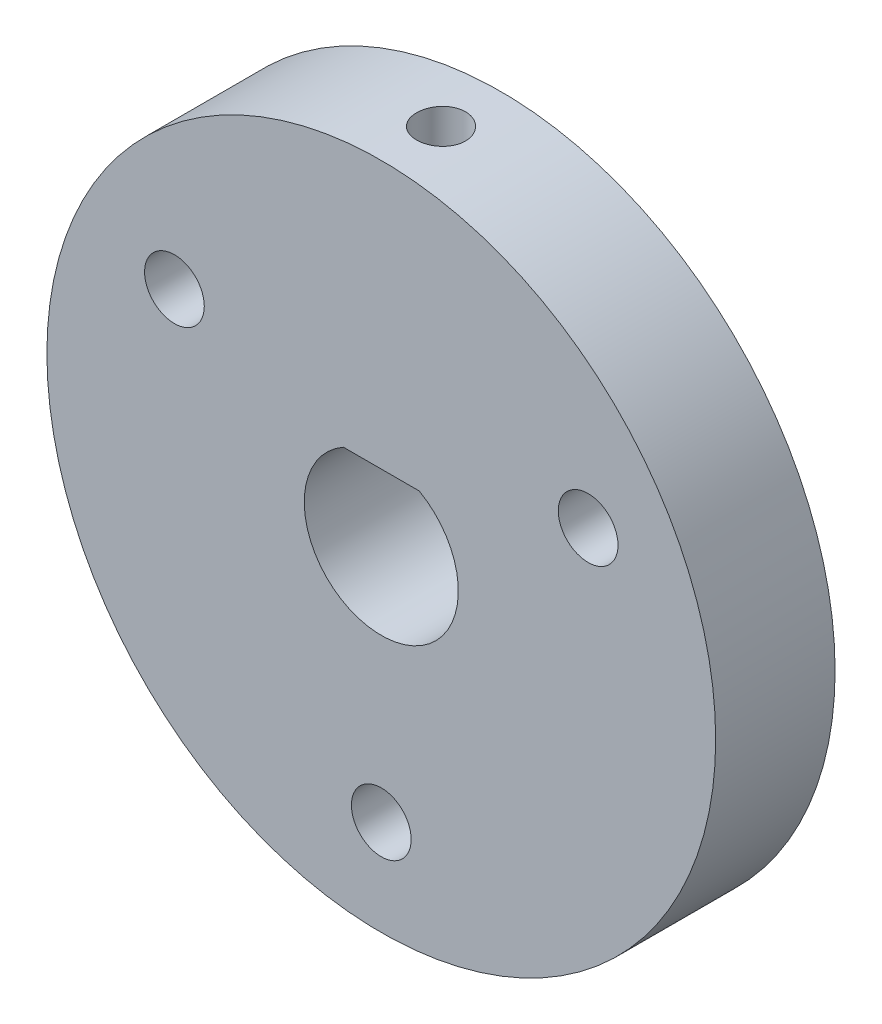
SolidWorks part; units mm, degrees
material "Plain Carbon Steel"
ref_plane "Front Plane" through (0, 0, 0) normal (0, 0, 1) x (1, 0, 0)
ref_plane "Top Plane" through (0, 0, 0) normal (0, 1, 0) x (1, 0, 0)
ref_plane "Right Plane" through (0, 0, 0) normal (1, 0, 0) x (0, 0, -1)
sketch "Sketch1" plane through (0, 0, 0) normal (0, 0, 1) x (1, 0, 0)
  line L0 (-1.5875, 2.8072) -> (1.5875, 2.8072)
  line L1 (-1.5875, 2.7496) -> (1.5875, 2.7496) construction
  line L2 (-5, 8.6603) -> (5, -8.6603) construction
  line L3 (-8.6603, -5) -> (8.6603, 5) construction
  line L4 (0, -1000) -> (0, 49000) construction
  circle A0 centre (0, 0) radius 3.225
  circle A1 centre (0, 0) radius 10 construction
  circle A2 centre (0, 0) radius 14
  circle A3 centre (0, 0) radius 3.175 construction
  point P15 (0, 0)
  dimension "D1" = 6.45
  dimension "D3" = 20
  dimension "D4" = 28
  dimension "D6" = 6.35
  dimension "D2" = 3.175
  dimension "D5" = 3.175
  dimension "D7" = 30
extrude "Boss-Extrude1" add sketch "Sketch1" along normal mid plane 5 contours A2 A0 | L0 A0
hole_wizard "M2.5 Clearance Hole1" positions "Sketch2" profile "Sketch3" hole size "M2.5" standard "ANSI Metric"
sketch "Sketch2" plane through (0, 0, 2.5) normal (0, 0, 1) x (1, 0, 0)
  point P9 (-5, 8.6603)
  point P12 (-8.6603, -5)
  point P15 (5, -8.6603)
  point P18 (8.6603, 5)
sketch "Sketch3" plane through (-5, 8.6603, 2.5) normal (1, 0, 0) x (0, -1, 0)
  line L0 (0, 0) -> (0, 5)
  line L1 (0, 5) -> (1.25, 5)
  line L2 (1.25, 5) -> (1.25, 0)
  line L5 (1.25, 0) -> (0, 0)
  line L11 (0, -6.35) -> (0, 107.95) construction
  dimension "Thru Hole Dia." = 2.5
  dimension "Thru Hole Depth" = 5
hole_wizard "M2.5 Clearance Hole2" positions "Sketch4" profile "Sketch5" hole size "M2.5" standard "ANSI Metric" end condition through all
sketch "Sketch4" plane through (0, 0, 2.5) normal (0, 0, 1) x (1, 0, 0)
  line L0 (0, -201000) -> (0, 249000) construction
  circle A0 centre (0, 0) radius 10 construction
  point P0 (0, -10)
sketch "Sketch5" plane through (0, -10, 2.5) normal (1, 0, 0) x (0, -1, 0)
  line L0 (0, 0) -> (0, 5)
  line L1 (0, 5) -> (1.25, 5)
  line L2 (1.25, 5) -> (1.25, 0)
  line L5 (1.25, 0) -> (0, 0)
  line L11 (0, -6.35) -> (0, 107.95) construction
  dimension "Thru Hole Dia." = 2.5
  dimension "Thru Hole Depth" = 5
pattern_circular "CirPattern1" count 3 over 360 about axis through (0, 0, 0) along (0, 0, 1) of "M2.5 Clearance Hole2"
hole_wizard "M2.5x0.45 Tapped Hole1" positions "Sketch6" profile "Sketch7" tap size "M2.5x0.45" standard "ANSI Metric"
sketch "Sketch6" plane through (0, 2.8072, 0) normal (0, -1, 0) x (-1, 0, 0)
  point P0 (0, 0)
sketch "Sketch7" plane through (0, 2.8072, 0) normal (1, 0, 0) x (0, 0, -1)
  line L0 (0, 0) -> (0, 11.1928)
  line L1 (0, 11.1928) -> (1.025, 11.1928)
  line L2 (1.025, 11.1928) -> (1.025, 0)
  line L5 (1.025, 0) -> (0, 0)
  line L11 (0, -6.35) -> (0, 107.95) construction
  dimension "Thru Tap Drill Dia." = 2.05
  dimension "Thru Tap Drill Depth" = 11.1928
cosmetic thread "Hole Thread1" parameters "D2"=2.5
